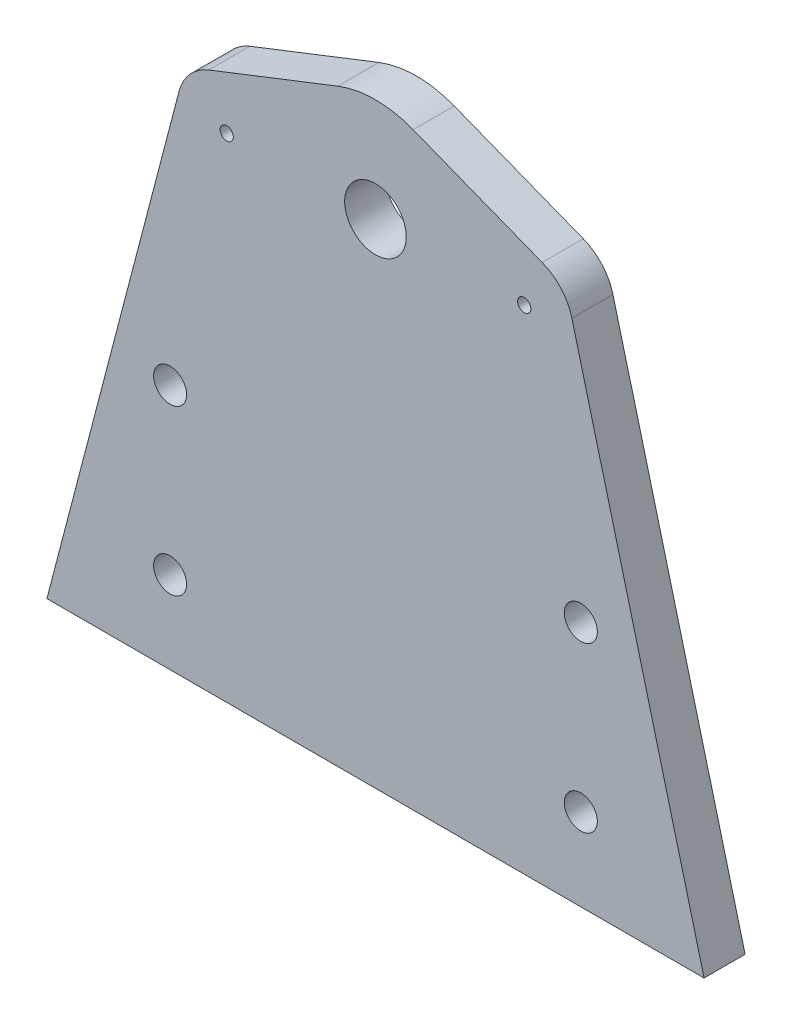
SolidWorks part; units mm, degrees
ref_plane "Front Plane" through (0, 0, 0) normal (0, 0, 1) x (1, 0, 0)
ref_plane "Top Plane" through (0, 0, 0) normal (0, 1, 0) x (1, 0, 0)
ref_plane "Right Plane" through (0, 0, 0) normal (1, 0, 0) x (0, 0, -1)
sketch "Sketch1" plane through (0, 0, 0) normal (0, 0, 1) x (1, 0, 0)
  line L0 (-25.7763, 7.0962) -> (-5.8296, 14.9002)
  line L1 (-50.8, -76.2) -> (50.8, -76.2)
  line L2 (5.8296, 14.9002) -> (25.7763, 7.0962)
  line L3 (-23, 0) -> (0, 0) construction
  line L4 (-31.75, -38.1) -> (0, -38.1) construction
  line L5 (0, -38.1) -> (31.75, -38.1) construction
  line L6 (0, 0) -> (0, -76.2) construction
  line L7 (-30.3722, 1.9276) -> (-50.8, -76.2)
  line L8 (30.3722, 1.9276) -> (50.8, -76.2)
  circle A0 centre (0, 0) radius 4.7625
  arc A1 (-5.8296, 14.9002) -> (5.8296, 14.9002) centre (0, 0) cw
  arc A2 (25.7763, 7.0962) -> (30.3722, 1.9276) centre (23, 0) cw
  arc A3 (-25.7763, 7.0962) -> (-30.3722, 1.9276) centre (-23, 0) ccw
  circle A5 centre (-31.75, -38.1) radius 1.5875
  circle A6 centre (31.75, -38.1) radius 1.5875
  circle A8 centre (-31.75, -63.5) radius 1.5875
  circle A10 centre (31.75, -63.5) radius 1.5875
  point P26 (-23, 0)
  point P27 (23, 0)
  dimension "D2" = 9.525
  dimension "D4" = 16
  dimension "D10" = 3.175
  dimension "D12" = 7.62
  dimension "D1" = 46
  dimension "D3" = 23
  dimension "D5" = 25.4
  dimension "D6" = 25.4
  dimension "D7" = 76.2
  dimension "D8" = 63.5
  dimension "D9" = 12.7
  dimension "D11" = 101.6
extrude "Boss-Extrude1" add sketch "Sketch1" along normal blind 6.35
hole_wizard "M2.5x0.45 Tapped Hole1" positions "Sketch3" profile "Sketch2" tap size "M2.5x0.45" standard "ANSI Metric" end condition through all
sketch "Sketch3" plane through (0, 0, 0) normal (0, 0, -1) x (-1, 0, 0)
  point P0 (-23, 0)
  point P3 (23, 0)
sketch "Sketch2" plane through (23, 0, 0) normal (1, 0, 0) x (0, 1, 0)
  line L0 (0, 0) -> (0, 6.35)
  line L1 (0, 6.35) -> (1.025, 6.35)
  line L2 (1.025, 6.35) -> (1.025, 0)
  line L5 (1.025, 0) -> (0, 0)
  line L11 (0, -6.35) -> (0, 107.95) construction
  dimension "Thread Major Dia." = 2.05
  dimension "Thru Tap Drill Depth" = 6.35
hole_wizard "1/4-20 Tapped Hole1" positions "Sketch5" profile "Sketch4" tap size "1/4-20" standard "ANSI Inch" end condition through all
sketch "Sketch5" plane through (0, 0, 6.35) normal (0, 0, 1) x (1, 0, 0)
  point P0 (-31.75, -38.1)
  point P3 (-31.75, -63.5)
  point P6 (31.75, -63.5)
  point P9 (31.75, -38.1)
sketch "Sketch4" plane through (-31.75, -38.1, 6.35) normal (1, 0, 0) x (0, -1, 0)
  line L0 (0, 0) -> (0, 6.35)
  line L1 (0, 6.35) -> (2.5527, 6.35)
  line L2 (2.5527, 6.35) -> (2.5527, 0)
  line L5 (2.5527, 0) -> (0, 0)
  line L11 (0, -6.35) -> (0, 107.95) construction
  dimension "Thread Major Dia." = 5.1054
  dimension "Thru Tap Drill Depth" = 6.35
equation "\"D3@Sketch1\"=\"D1@Sketch1\"/2"
